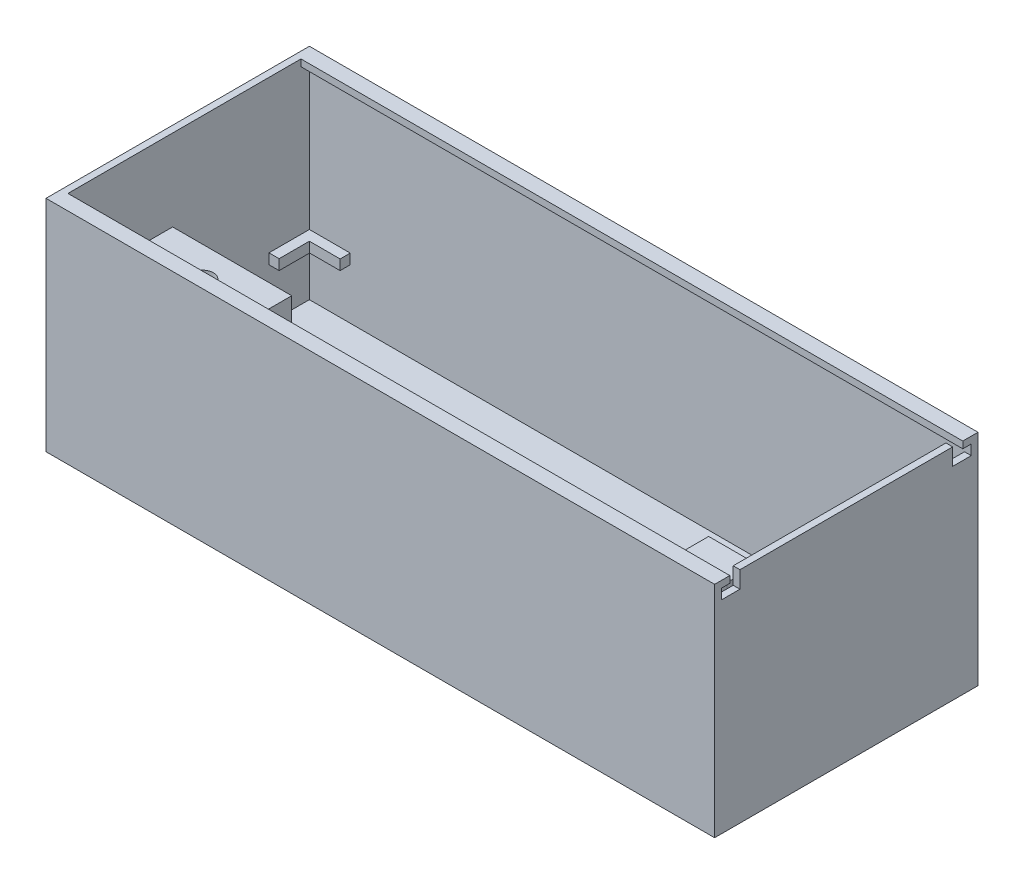
SolidWorks part; units mm, degrees
material "ABS"
ref_plane "Front" through (0, 0, 0) normal (0, 0, 1) x (1, 0, 0)
ref_plane "Top" through (0, 0, 0) normal (0, 1, 0) x (1, 0, 0)
ref_plane "Right" through (0, 0, 0) normal (1, 0, 0) x (0, 0, -1)
sketch "Sketch2" plane through (0, 0, 0) normal (0, 1, 0) x (1, 0, 0)
  line L1 (-99, -39) -> (99, -39)
  line L2 (-99, -39) -> (-99, 39)
  line L3 (-99, 39) -> (99, 39)
  line L4 (99, -39) -> (99, 39)
  line L5 (-99, -39) -> (99, 39) construction
  line L6 (-99, 39) -> (99, -39) construction
  point P0 (0, 0)
  dimension "D1" = 78
  dimension "D2" = 198
extrude "Boss-Extrude1" add sketch "Sketch2" along normal blind 50 and the other way blind 15
shell "Shell1" thickness 2
fillet "Fillet1" [suppressed] radius 10
sketch "Sketch3" plane through (-97, 0, 0) normal (1, 0, 0) x (0, 0, -1)
  line L0 (0, -15) -> (0, 50) construction
  line L1 (-37, 50) -> (-34.5, 50)
  line L2 (-37, 50) -> (-37, 48)
  line L3 (-37, 48) -> (-34.5, 48)
  line L4 (-34.5, 50) -> (-34.5, 48)
  line L5 (39, -15) -> (-39, -15) construction
  line L6 (37, 50) -> (-37, 50) construction
  line L7 (34.5, 50) -> (34.5, 48)
  line L8 (37, 48) -> (34.5, 48)
  line L9 (37, 50) -> (37, 48)
  line L10 (37, 50) -> (34.5, 50)
  dimension "D1" = 2.5
  dimension "D2" = 2
extrude "Boss-Extrude2" add sketch "Sketch3" along normal up to next
sketch "Sketch4" plane through (97, 0, 0) normal (-1, 0, 0) x (0, 0, 1)
  line L0 (-37, 48) -> (-37, 45)
  line L1 (-37, 48) -> (-37, -13) construction
  line L2 (-37, 45) -> (-31.5, 45)
  line L3 (-31.5, 45) -> (-31.5, 50)
  line L4 (34.5, 50) -> (-34.5, 50) construction
  line L5 (-31.5, 50) -> (-34.5, 50)
  line L6 (-34.5, 50) -> (-34.5, 48)
  line L7 (-37, 48) -> (-34.5, 48) construction
  line L8 (-34.5, 48) -> (-34.5, 50) construction
  line L9 (-34.5, 48) -> (-37, 48)
  line L10 (0, -15) -> (0, 50) construction
  line L11 (39, -15) -> (-39, -15) construction
  line L12 (34.5, 48) -> (37, 48)
  line L13 (34.5, 50) -> (34.5, 48)
  line L14 (31.5, 50) -> (34.5, 50)
  line L15 (31.5, 45) -> (31.5, 50)
  line L16 (37, 45) -> (31.5, 45)
  line L17 (37, 48) -> (37, 45)
  dimension "D1" = 3
  dimension "D2" = 3
extrude "Cut-Extrude1" cut sketch "Sketch4" against normal up to next
sketch "Croquis1" plane through (0, -13, 0) normal (0, 1, 0) x (1, 0, 0)
  line L0 (97, -37) -> (97, 37) construction
  line L1 (97, -29.5) -> (61.735, -29.5)
  line L2 (97, -29.5) -> (97, -3.5)
  line L3 (97, -3.5) -> (61.735, -3.5)
  line L4 (61.735, -29.5) -> (61.735, -3.5)
  line L6 (-97, -37) -> (97, -37) construction
  dimension "D1" = 35.265
  dimension "D2" = 26
  dimension "D3" = 7.5
extrude "Saliente-Extruir1" add sketch "Croquis1" along normal blind 38.9
mirror "Simetría1" about plane through (0, 0, 0) normal (1, 0, 0) of "Saliente-Extruir1"
sketch "Croquis2" plane through (0, 25.9, 0) normal (0, 1, 0) x (1, 0, 0)
  line L0 (79.235, -12.375) -> (79.235, -20.625) construction
  line L1 (82.41, -12.375) -> (82.41, -20.625)
  line L2 (76.06, -12.375) -> (76.06, -20.625)
  line L3 (97, -29.5) -> (97, -3.5) construction
  line L4 (79.235, -23.8) -> (79.235, -29.5) construction
  line L5 (61.735, -29.5) -> (97, -29.5) construction
  arc A0 (82.41, -12.375) -> (76.06, -12.375) centre (79.235, -12.375) ccw
  arc A1 (76.06, -20.625) -> (82.41, -20.625) centre (79.235, -20.625) ccw
  point P2 (79.235, -16.5)
  point P7 (79.235, -9.2)
  point P8 (79.235, -23.8)
  dimension "D1" = 14.6
  dimension "D2" = 6.35
  dimension "D3" = 14.59
  dimension "D4" = 5.7
extrude "Cortar-Extruir1" cut sketch "Croquis2" against normal blind 2
mirror "Simetría2" about plane through (0, 0, 0) normal (1, 0, 0) of "Cortar-Extruir1"
sketch "Croquis3" plane through (0, 23.9, 0) normal (0, 1, 0) x (1, 0, 0)
  line L0 (79.235, -13.2) -> (79.235, -19.8) construction
  line L1 (80.835, -13.2) -> (80.835, -19.8)
  line L2 (77.635, -13.2) -> (77.635, -19.8)
  line L3 (76.06, -12.375) -> (76.06, -20.625) construction
  arc A0 (80.835, -13.2) -> (77.635, -13.2) centre (79.235, -13.2) ccw
  arc A1 (77.635, -19.8) -> (80.835, -19.8) centre (79.235, -19.8) ccw
  point P3 (79.235, -16.5)
  point P11 (76.06, -16.5)
  dimension "D1" = 6.6
  dimension "D2" = 3.2
extrude "Cortar-Extruir2" cut sketch "Croquis3" against normal blind 30
mirror "Simetría3" about plane through (0, 0, 0) normal (1, 0, 0) of "Cortar-Extruir2"
sketch "Croquis5" plane through (61.735, 0, 0) normal (-1, 0, 0) x (0, 0, 1)
  line L0 (29.5, 25.9) -> (29.5, -13) construction
  line L1 (3.5, -13) -> (29.5, -13)
  line L2 (3.5, -13) -> (3.5, 2)
  line L3 (3.5, 2) -> (29.5, 2)
  line L4 (29.5, -13) -> (29.5, 2)
  dimension "D1" = 15
extrude "Cortar-Extruir3" cut sketch "Croquis5" against normal up to surface (35.265 mm away) up to face at (97, 23.3167, 5.5)
sketch "Croquis6" plane through (61.735, 0, 0) normal (-1, 0, 0) x (0, 0, 1)
  line L0 (29.5, 2) -> (3.5, 2) construction
  line L1 (10.5, 2) -> (22.5, 2)
  line L2 (10.5, 2) -> (10.5, 5)
  line L3 (10.5, 5) -> (22.5, 5)
  line L4 (22.5, 2) -> (22.5, 5)
  line L5 (3.5, 25.9) -> (3.5, 2) construction
  line L6 (3.5, 25.9) -> (29.5, 25.9) construction
  line L7 (29.5, 25.9) -> (3.5, 25.9) construction
  dimension "D1" = 12
  dimension "D2" = 7
  dimension "D3" = 3
extrude "Saliente-Extruir2" add sketch "Croquis6" along normal blind 3
sketch "Croquis7" plane through (-61.735, 0, 0) normal (1, 0, 0) x (0, 0, -1)
  line L0 (-29.5, 25.9) -> (-29.5, -13) construction
  line L1 (-3.5, -13) -> (-29.5, -13)
  line L2 (-3.5, -13) -> (-3.5, 2)
  line L3 (-3.5, 2) -> (-29.5, 2)
  line L4 (-29.5, -13) -> (-29.5, 2)
  dimension "D1" = 15
extrude "Cortar-Extruir4" cut sketch "Croquis7" against normal up to surface (35.265 mm away) up to face at (-97, 24.3167, 5.5)
mirror "Simetría7" about plane through (0, 0, 0) normal (1, 0, 0) of "Saliente-Extruir2"
sketch "Croquis8" plane through (0, 0, -37) normal (0, 0, 1) x (1, 0, 0)
  line L0 (97, -13) -> (97, 45) construction
  line L1 (85, 5) -> (97, 5)
  line L2 (85, 5) -> (85, 2)
  line L3 (85, 2) -> (97, 2)
  line L4 (97, 5) -> (97, 2)
  line L5 (99, 50) -> (-97, 50) construction
  dimension "D1" = 12
  dimension "D2" = 3
  dimension "D3" = 45
extrude "Saliente-Extruir4" add sketch "Croquis8" along normal blind 3
sketch "Croquis10" plane through (97, 0, 0) normal (-1, 0, 0) x (0, 0, 1)
  line L0 (-37, 5) -> (-37, 45) construction
  line L1 (-37, 2) -> (-24.9901, 2)
  line L2 (-37, 2) -> (-37, 5)
  line L3 (-37, 5) -> (-24.9901, 5)
  line L4 (-24.9901, 2) -> (-24.9901, 5)
  line L5 (31.5, 50) -> (-31.5, 50) construction
  dimension "D1" = 48
  dimension "D2" = 3
extrude "Saliente-Extruir5" add sketch "Croquis10" along normal blind 3
sketch "Croquis11" plane through (0, 0, -37) normal (0, 0, 1) x (1, 0, 0)
  line L0 (-97, -13) -> (-97, 48) construction
  line L1 (-97, 5) -> (-84.9018, 5)
  line L2 (-97, 5) -> (-97, 2)
  line L3 (-97, 2) -> (-84.9018, 2)
  line L4 (-84.9018, 5) -> (-84.9018, 2)
  line L5 (99, 50) -> (-97, 50) construction
  dimension "D1" = 45
  dimension "D2" = 3
extrude "Saliente-Extruir6" add sketch "Croquis11" along normal blind 3
sketch "Croquis12" plane through (-97, 0, 0) normal (1, 0, 0) x (0, 0, -1)
  line L0 (37, 5) -> (37, 48) construction
  line L1 (37, 5) -> (25.0372, 5)
  line L2 (37, 5) -> (37, 1.9355)
  line L3 (37, 1.9355) -> (25.0372, 1.9355)
  line L4 (25.0372, 5) -> (25.0372, 1.9355)
  line L5 (34.5, 50) -> (-34.5, 50) construction
  dimension "D1" = 45
extrude "Saliente-Extruir7" add sketch "Croquis12" along normal blind 3
